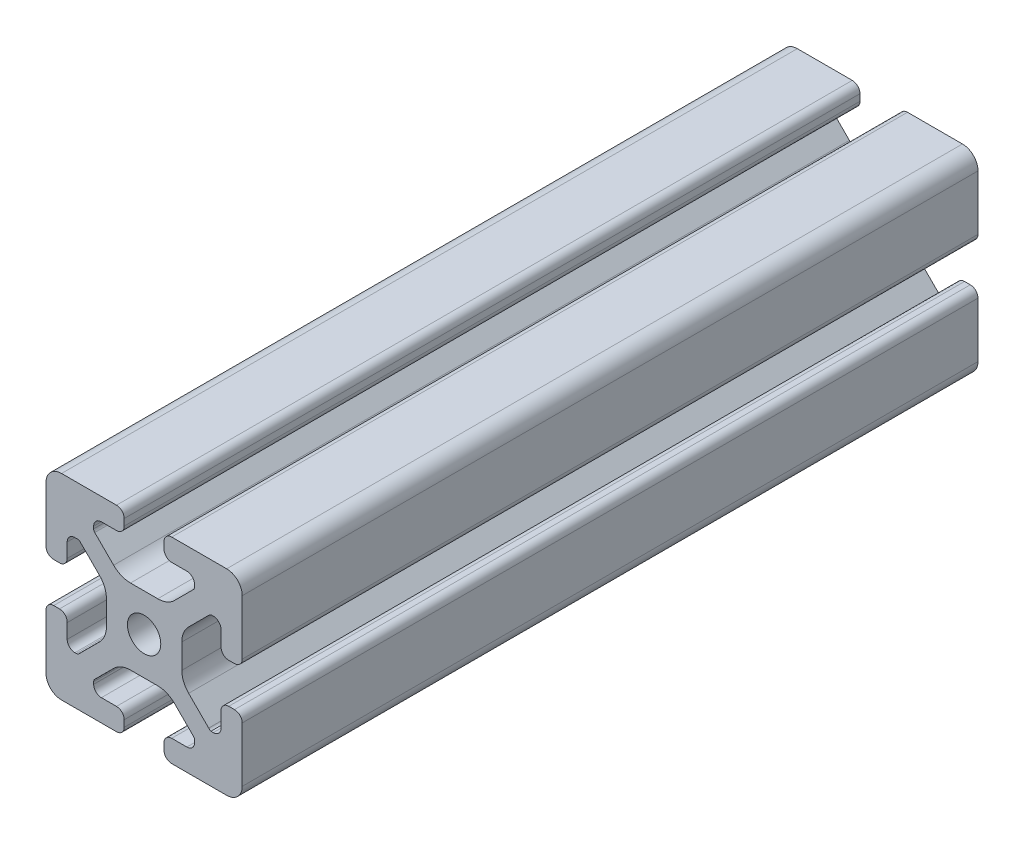
SolidWorks part; units mm, degrees
material "6105-T5 Aluminum"
ref_plane "Front Plane" through (0, 0, 0) normal (0, 0, 1) x (1, 0, 0)
ref_plane "Top Plane" through (0, 0, 0) normal (0, 1, 0) x (1, 0, 0)
ref_plane "Right Plane" through (0, 0, 0) normal (1, 0, 0) x (0, 0, -1)
sketch "Sketch1" plane through (0, 0, 0) normal (0, 0, 1) x (1, 0, 0)
  line L0 (0, 19.7407) -> (0, -19.7407) construction
  line L1 (19.0335, 0) -> (-20.7246, 0) construction
  line L2 (-8.715, -15.5246) -> (-5.63, -15.5246)
  line L3 (-10.285, -13.9546) -> (-10.285, -13.4925)
  line L4 (-6.2171, -9.1098) -> (-10.0624, -12.9551)
  line L5 (2.7773, -7.685) -> (-2.7773, -7.685)
  line L6 (10.0624, -12.9551) -> (6.2171, -9.1098)
  line L7 (10.285, -13.9546) -> (10.285, -13.4925)
  line L8 (5.63, -15.5246) -> (8.715, -15.5246)
  line L9 (4.06, -18.43) -> (4.06, -17.0946)
  line L10 (-4.06, -18.43) -> (-4.06, -17.0946)
  line L11 (15.68, -8.7154) -> (15.68, -5.63)
  line L12 (-14.11, -10.2854) -> (-13.8169, -10.2854)
  line L13 (20, -16.83) -> (20, -5.63)
  line L14 (20, 5.63) -> (20, 13.0011)
  line L15 (-16.83, 20) -> (-5.63, 20)
  line L16 (5.63, 20) -> (12.9796, 20)
  line L18 (-8.715, 15.5246) -> (-5.63, 15.5246)
  line L19 (-20, -17.0184) -> (-20, -5.7579)
  line L20 (-20, 5.573) -> (-20, 13.0045)
  line L21 (-15.68, -8.7154) -> (-15.68, -5.7579)
  line L23 (-16.6746, -20) -> (-5.63, -20)
  line L24 (5.63, -20) -> (13, -20)
  line L53 (14.11, -10.2854) -> (13.6201, -10.2854)
  line L54 (13.1637, -9.947) -> (9.0762, -5.8595)
  line L55 (7.685, -2.5008) -> (7.685, 2.5008)
  line L56 (9.0762, 5.8595) -> (13.2795, 10.0628)
  line L57 (13.8169, 10.2854) -> (14.11, 10.2854)
  line L58 (15.68, 8.7154) -> (15.68, 5.63)
  line L59 (17.25, 4.06) -> (18.43, 4.06)
  line L61 (20, 13.0011) -> (20, 16.83)
  line L62 (16.83, 20) -> (12.9796, 20)
  line L64 (4.06, 18.43) -> (4.06, 17.0946)
  line L65 (5.63, 15.5246) -> (8.715, 15.5246)
  line L66 (10.285, 13.9546) -> (10.285, 13.4925)
  line L67 (10.0624, 12.9551) -> (6.2171, 9.1098)
  line L68 (2.7773, 7.685) -> (-2.7773, 7.685)
  line L69 (-6.2171, 9.1098) -> (-10.0624, 12.9551)
  line L70 (-10.285, 13.4925) -> (-10.285, 13.9546)
  line L72 (-4.06, 17.0946) -> (-4.06, 18.43)
  line L75 (-20, 16.83) -> (-20, 13.0045)
  line L77 (-18.43, 4.003) -> (-17.25, 4.003)
  line L78 (-15.68, 5.573) -> (-15.68, 8.4757)
  line L79 (-14.0552, 10.0447) -> (-13.7199, 10.033)
  line L80 (-13.0405, 9.8238) -> (-9.0762, 5.8595)
  line L81 (-7.685, 2.5008) -> (-7.685, -2.5008)
  line L82 (-9.0762, -5.8595) -> (-13.2795, -10.0628)
  line L85 (-17.25, -4.1204) -> (-18.43, -4.1204)
  line L100 (13, -20) -> (16.83, -20)
  line L103 (18.43, -4.06) -> (17.25, -4.06)
  arc A0 (-5.63, -15.5246) -> (-4.06, -17.0946) centre (-5.63, -17.0946) cw
  arc A1 (-8.715, -15.5246) -> (-10.285, -13.9546) centre (-8.715, -13.9546) cw
  arc A2 (-10.285, -13.4925) -> (-10.0624, -12.9551) centre (-9.525, -13.4925) cw
  arc A3 (-6.2171, -9.1098) -> (-2.7773, -7.685) centre (-2.7773, -12.5496) cw
  arc A4 (2.7773, -7.685) -> (6.2171, -9.1098) centre (2.7773, -12.5496) cw
  arc A5 (10.0624, -12.9551) -> (10.285, -13.4925) centre (9.525, -13.4925) cw
  arc A6 (10.285, -13.9546) -> (8.715, -15.5246) centre (8.715, -13.9546) cw
  arc A7 (4.06, -17.0946) -> (5.63, -15.5246) centre (5.63, -17.0946) cw
  arc A8 (5.63, -20) -> (4.06, -18.43) centre (5.63, -18.43) cw
  arc A9 (-4.06, -18.43) -> (-5.63, -20) centre (-5.63, -18.43) cw
  circle A45 centre (0, 0) radius 3.4
  arc A46 (17.25, -4.06) -> (15.68, -5.63) centre (17.25, -5.63) ccw
  arc A47 (14.11, -10.2854) -> (15.68, -8.7154) centre (14.11, -8.7154) ccw
  arc A48 (13.1637, -9.947) -> (13.6201, -10.2854) centre (13.8117, -9.55) ccw
  arc A49 (7.685, -2.5008) -> (9.0762, -5.8595) centre (12.435, -2.5008) ccw
  arc A50 (9.0762, 5.8595) -> (7.685, 2.5008) centre (12.435, 2.5008) ccw
  arc A51 (13.8169, 10.2854) -> (13.2795, 10.0628) centre (13.8169, 9.5254) ccw
  arc A52 (15.68, 8.7154) -> (14.11, 10.2854) centre (14.11, 8.7154) ccw
  arc A53 (15.68, 5.63) -> (17.25, 4.06) centre (17.25, 5.63) ccw
  arc A54 (18.43, 4.06) -> (20, 5.63) centre (18.43, 5.63) ccw
  arc A55 (20, 16.83) -> (16.83, 20) centre (16.83, 16.83) ccw
  arc A56 (5.63, 20) -> (4.06, 18.43) centre (5.63, 18.43) ccw
  arc A57 (4.06, 17.0946) -> (5.63, 15.5246) centre (5.63, 17.0946) ccw
  arc A58 (10.285, 13.9546) -> (8.715, 15.5246) centre (8.715, 13.9546) ccw
  arc A59 (10.0624, 12.9551) -> (10.285, 13.4925) centre (9.525, 13.4925) ccw
  arc A60 (2.7773, 7.685) -> (6.2171, 9.1098) centre (2.7773, 12.5496) ccw
  arc A61 (-6.2171, 9.1098) -> (-2.7773, 7.685) centre (-2.7773, 12.5496) ccw
  arc A62 (-10.285, 13.4925) -> (-10.0624, 12.9551) centre (-9.525, 13.4925) ccw
  arc A63 (-8.715, 15.5246) -> (-10.285, 13.9546) centre (-8.715, 13.9546) ccw
  arc A64 (-5.63, 15.5246) -> (-4.06, 17.0946) centre (-5.63, 17.0946) ccw
  arc A65 (-4.06, 18.43) -> (-5.63, 20) centre (-5.63, 18.43) ccw
  arc A66 (-16.83, 20) -> (-20, 16.83) centre (-16.83, 16.83) ccw
  arc A67 (-20, 5.573) -> (-18.43, 4.003) centre (-18.43, 5.573) ccw
  arc A68 (-17.25, 4.003) -> (-15.68, 5.573) centre (-17.25, 5.573) ccw
  arc A69 (-14.0552, 10.0447) -> (-15.68, 8.4757) centre (-14.11, 8.4757) ccw
  arc A70 (-13.0405, 9.8238) -> (-13.7199, 10.033) centre (-13.5779, 9.2864) ccw
  arc A71 (-7.685, 2.5008) -> (-9.0762, 5.8595) centre (-12.435, 2.5008) ccw
  arc A72 (-9.0762, -5.8595) -> (-7.685, -2.5008) centre (-12.435, -2.5008) ccw
  arc A73 (-13.8169, -10.2854) -> (-13.2795, -10.0628) centre (-13.8169, -9.5254) ccw
  arc A74 (-15.68, -8.7154) -> (-14.11, -10.2854) centre (-14.11, -8.7154) ccw
  arc A75 (-15.68, -5.7579) -> (-17.25, -4.1204) centre (-17.2485, -5.6904) ccw
  arc A76 (-18.43, -4.1204) -> (-20, -5.7579) centre (-18.4315, -5.6904) ccw
  arc A77 (-20, -17.0184) -> (-16.6746, -20) centre (-16.8354, -16.8341) ccw
  arc A88 (16.83, -20) -> (20, -16.83) centre (16.83, -16.83) ccw
  arc A89 (20, -5.63) -> (18.43, -4.06) centre (18.43, -5.63) ccw
  dimension "D2" = 6.8
  dimension "D7" = 20.57
  dimension "D1" = 40
  dimension "D3" = 4.32
  dimension "D4" = 15.37
  dimension "D5" = 20
  dimension "D6" = 4.32
  dimension "D9" = 15.37
extrude "Extrude1" add sketch "Sketch1" against normal blind 150
